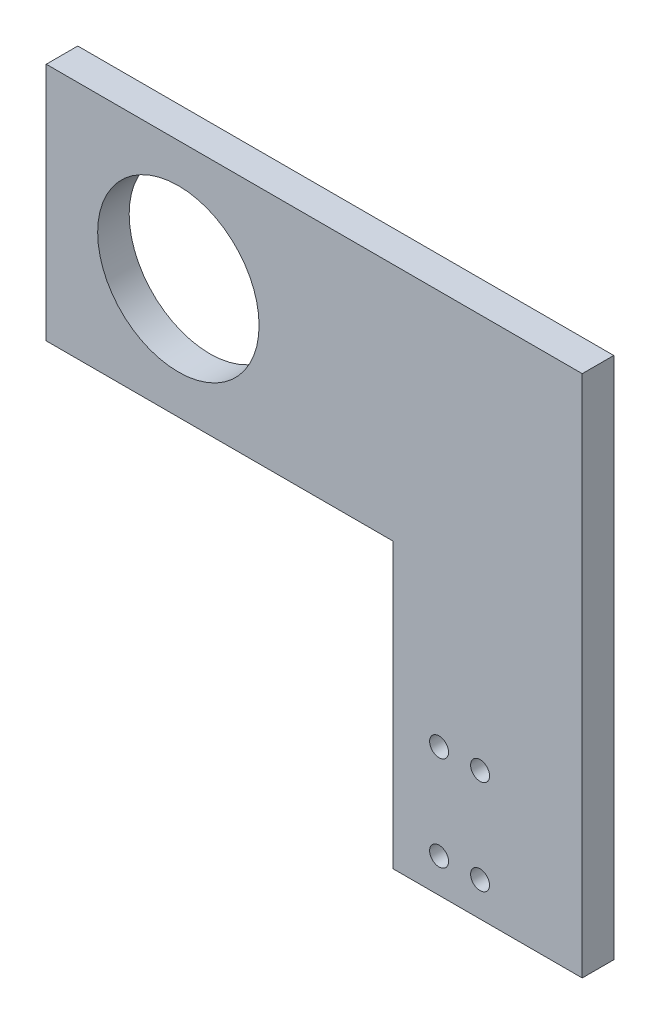
SolidWorks part; units mm, degrees
ref_plane "前视基准面" through (0, 0, 0) normal (0, 0, 1) x (1, 0, 0)
ref_plane "上视基准面" through (0, 0, 0) normal (0, 1, 0) x (1, 0, 0)
ref_plane "右视基准面" through (0, 0, 0) normal (1, 0, 0) x (0, 0, -1)
sketch "草图6" plane through (0, 0, 0) normal (0, 0, 1) x (1, 0, 0)
  line L0 (2402.4805, 4706.1072) -> (2402.4805, 4661.1072)
  line L1 (2432.4805, 4661.1072) -> (2432.4805, 4744.1072)
  line L2 (2432.4805, 4744.1072) -> (2347.4805, 4744.1072)
  line L3 (2402.4805, 4706.1072) -> (2347.4805, 4706.1072)
  line L4 (2347.4805, 4706.1072) -> (2347.4805, 4744.1072)
  line L5 (2402.4805, 4661.1072) -> (2432.4805, 4661.1072)
  circle A0 centre (2409.7793, 4666.5072) radius 1.5
  circle A1 centre (2409.7793, 4681.5072) radius 1.5
  circle A2 centre (2416.2793, 4666.5072) radius 1.5
  circle A3 centre (2416.2793, 4681.5072) radius 1.5
  circle A4 centre (2368.4335, 4725.1072) radius 12.8
extrude "凸台-拉伸5" add sketch "草图6" along normal blind 5
